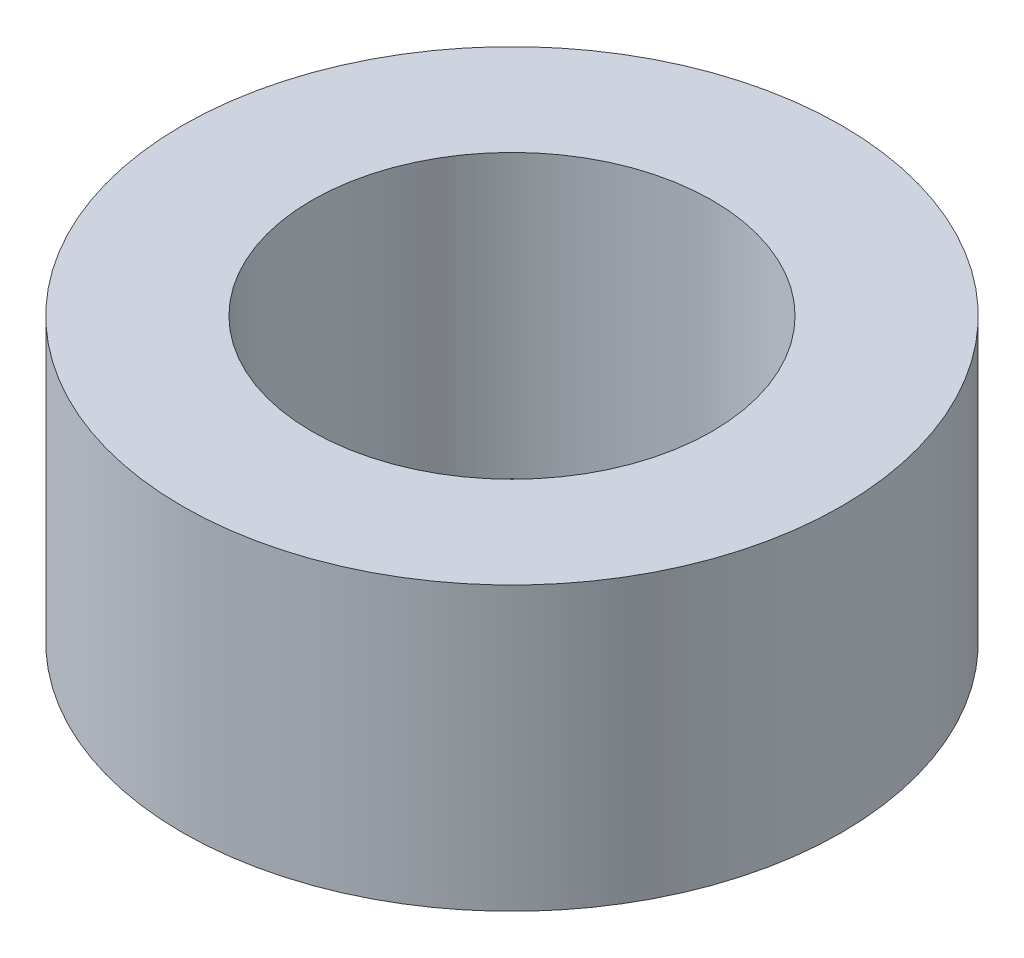
SolidWorks part; units mm, degrees
ref_plane "Front Plane" through (0, 0, 0) normal (0, 0, 1) x (1, 0, 0)
ref_plane "Top Plane" through (0, 0, 0) normal (0, 1, 0) x (1, 0, 0)
ref_plane "Right Plane" through (0, 0, 0) normal (1, 0, 0) x (0, 0, -1)
sketch "Sketch1" plane through (0, 0, 0) normal (0, 1, 0) x (1, 0, 0)
  circle A0 centre (0, 0) radius 3.5
  circle A1 centre (0, 0) radius 2.125
  dimension "D1" = 4.25
  dimension "D2" = 7
extrude "Boss-Extrude1" add sketch "Sketch1" along normal blind 3
